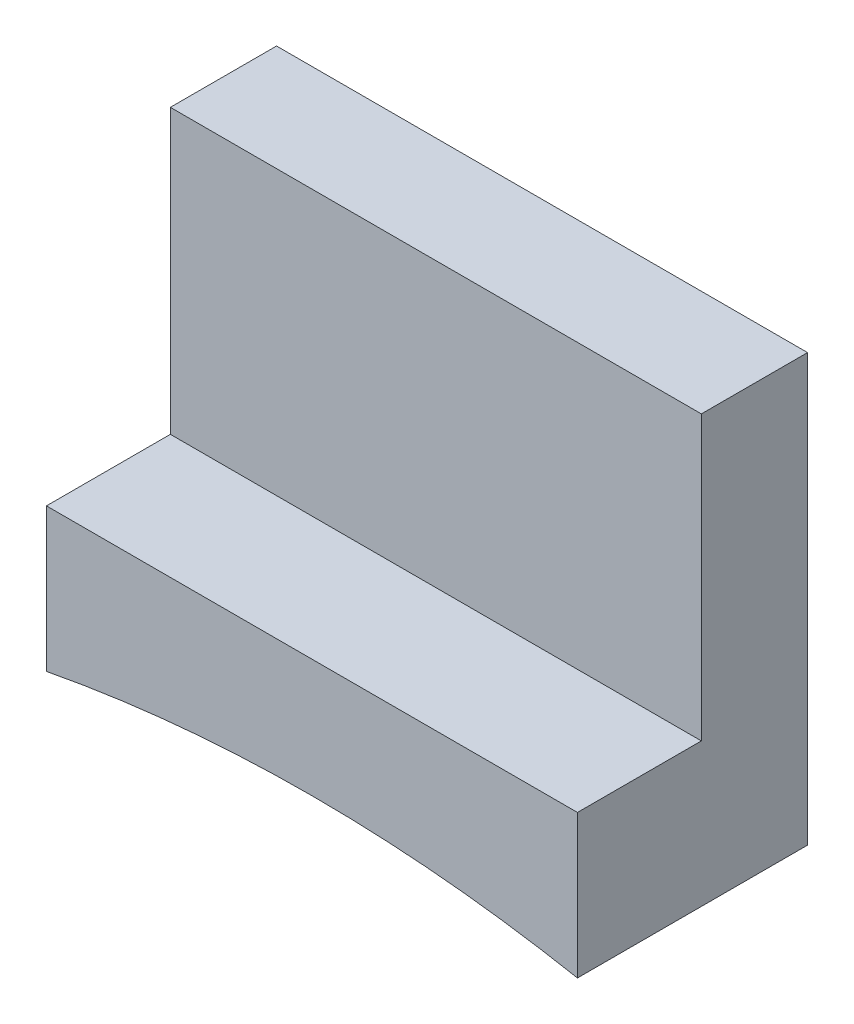
SolidWorks part; units mm, degrees
ref_plane "Front Plane" through (0, 0, 0) normal (0, 0, 1) x (1, 0, 0)
ref_plane "Top Plane" through (0, 0, 0) normal (0, 1, 0) x (1, 0, 0)
ref_plane "Right Plane" through (0, 0, 0) normal (1, 0, 0) x (0, 0, -1)
sketch "Sketch1" plane through (0, 0, 0) normal (0, 1, 0) x (1, 0, 0)
  line L1 (0, 0) -> (15, 0)
  line L2 (0, 0) -> (0, 6.5)
  line L3 (0, 6.5) -> (15, 6.5)
  line L4 (15, 0) -> (15, 6.5)
  dimension "D1" = 15
  dimension "D2" = 6.5
extrude "Boss-Extrude1" add sketch "Sketch1" along normal blind 1
sketch "Sketch2" plane through (0, 0, 0) normal (0, 0, 1) x (1, 0, 0)
  line L0 (0, 0) -> (0, -3.0503)
  line L1 (15, 0) -> (15, -3.0503)
  line L2 (0, 1) -> (0, 0) construction
  arc A0 (15, 0) -> (0, 0) centre (7.5, -42.3409) ccw
  arc A1 (15, -3.0503) -> (0, -3.0503) centre (7.5, -42.3409) ccw
  dimension "D1" = 86
  dimension "D2" = 3
extrude "Boss-Extrude2" add sketch "Sketch2" along normal blind 6.5 from surface at -6.5 starting at face at (7.5, 0.5, -6.5)
sketch "Sketch3" plane through (0, 1, 0) normal (0, 1, 0) x (1, 0, 0)
  line L6 (15, 0) -> (15, 6.5) construction
  line L8 (0, 6.5) -> (15, 6.5)
  line L9 (0, 6.5) -> (0, 3.5)
  line L10 (0, 3.5) -> (15, 3.5)
  line L11 (15, 6.5) -> (15, 3.5)
  dimension "D1" = 3
extrude "Boss-Extrude3" add sketch "Sketch3" along normal blind 8
